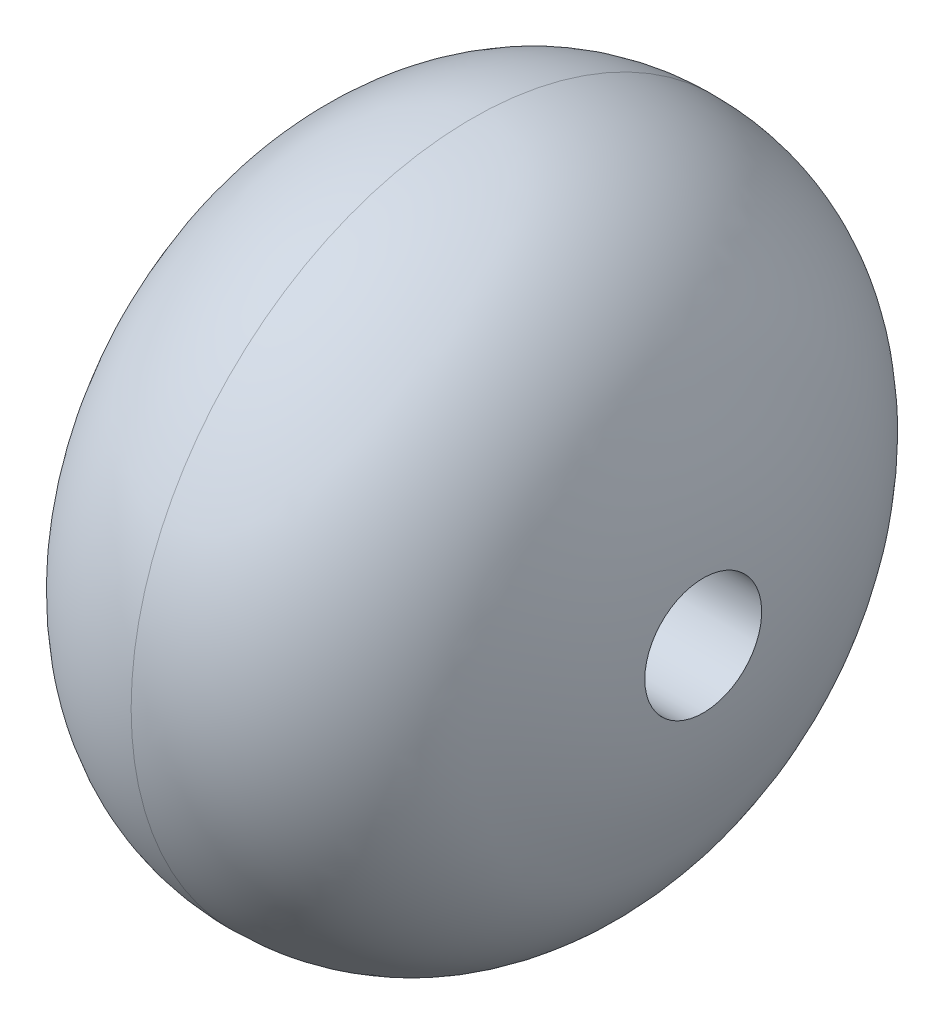
SolidWorks part; units mm, degrees
other "Caméra1"
material "Plastique personnalisé"
ref_plane "Plan de face" through (0, 0, 0) normal (0, 0, 1) x (1, 0, 0)
ref_plane "Plan de dessus" through (0, 0, 0) normal (0, 1, 0) x (1, 0, 0)
ref_plane "Plan de droite" through (0, 0, 0) normal (1, 0, 0) x (0, 0, -1)
sketch "Esquisse1" plane through (0, 0, 0) normal (0, 0, 1) x (1, 0, 0)
  line L0 (0, 0) -> (0, 17.5) construction
  line L1 (-12, 0) -> (12, 0)
  line L2 (12, 4.2502) -> (12, -4.2502) construction
  line L3 (-4.0505, 17.5) -> (4.0505, 17.5) construction
  spline S0 degree 3 poles (12, 0) (12, 4.3912) (11.1656, 7.4492) (8.8205, 13.5263) (5.0562, 17.5) (0, 17.5) knots 0 0 0 0 0.473704 0.573704 1 1 1 1
  spline S1 degree 3 poles (-12, 0) (-12, 4.3912) (-11.1656, 7.4492) (-8.8205, 13.5263) (-5.0562, 17.5) (0, 17.5) knots 0 0 0 0 0.473704 0.573704 1 1 1 1
  dimension "D1" = 17.5
  dimension "D2" = 12
revolve "Révolution1" add sketch "Esquisse1" angle 360 about L1
sketch "Esquisse2" plane through (0, 0, 0) normal (1, 0, 0) x (0, 0, -1)
  circle A0 centre (0, 0) radius 3
  dimension "D1" = 6
extrude "Enlèv. mat.-Extru.1" cut sketch "Esquisse2" against normal through all both and the other way through all
